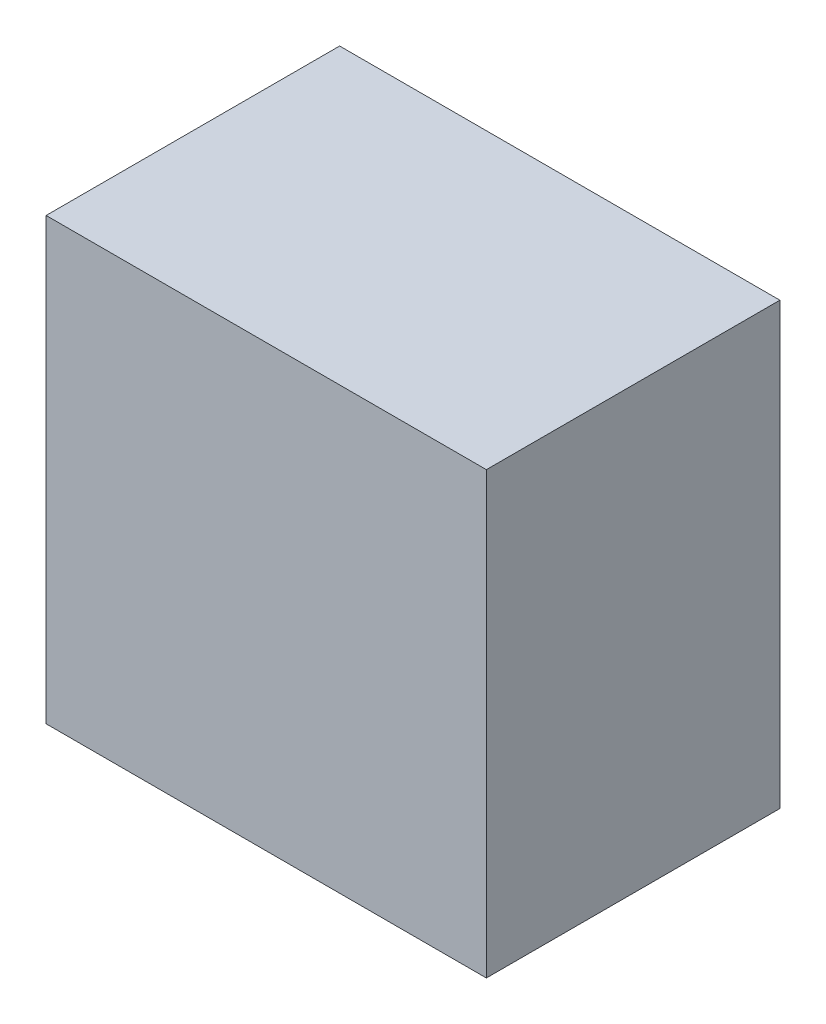
SolidWorks part; units mm, degrees
ref_plane "前视基准面" through (0, 0, 0) normal (0, 0, 1) x (1, 0, 0)
ref_plane "上视基准面" through (0, 0, 0) normal (0, 1, 0) x (1, 0, 0)
ref_plane "右视基准面" through (0, 0, 0) normal (1, 0, 0) x (0, 0, -1)
sketch "草图1" plane through (0, 0, 0) normal (0, 0, 1) x (1, 0, 0)
  line L1 (-15, 15) -> (15, 15)
  line L2 (-15, 15) -> (-15, -15)
  line L3 (-15, -15) -> (15, -15)
  line L4 (15, 15) -> (15, -15)
  line L5 (-15, 15) -> (15, -15) construction
  line L6 (-15, -15) -> (15, 15) construction
  point P0 (0, 0)
  dimension "D1" = 30
  dimension "D2" = 30
extrude "凸台-拉伸1" add sketch "草图1" along normal blind 20 contours L2 L3 L4 L1
